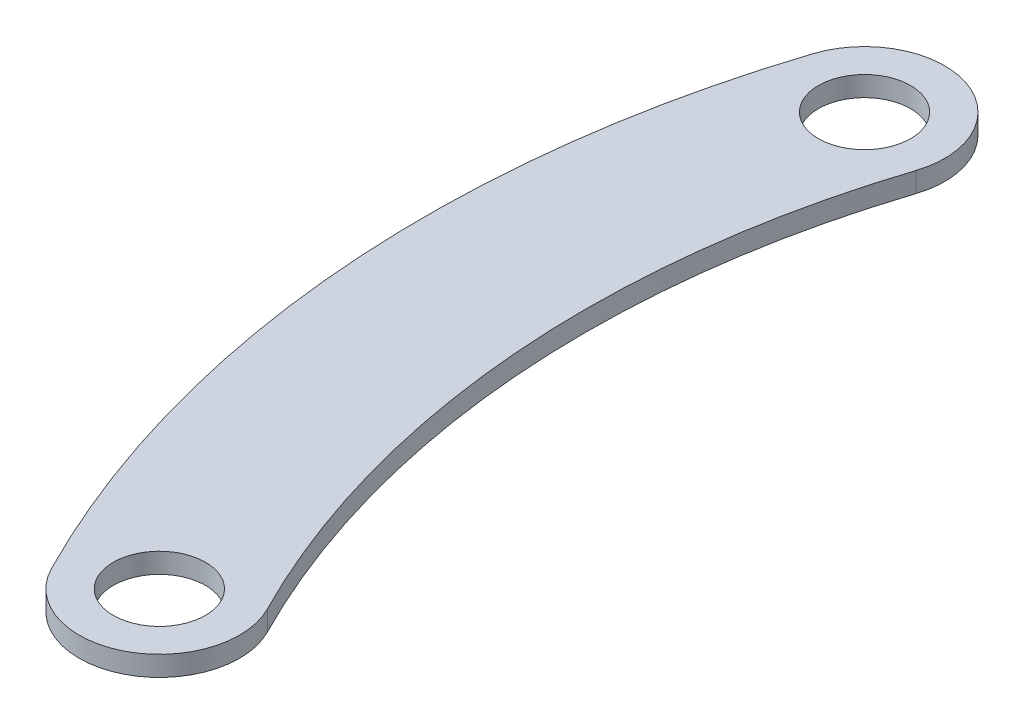
SolidWorks part; units mm, degrees
ref_plane "Front Plane" through (0, 0, 0) normal (0, 0, 1) x (1, 0, 0)
ref_plane "Top Plane" through (0, 0, 0) normal (0, 1, 0) x (1, 0, 0)
ref_plane "Right Plane" through (0, 0, 0) normal (1, 0, 0) x (0, 0, -1)
sketch "Sketch1" plane through (0, 0, 0) normal (0, 1, 0) x (1, 0, 0)
  line L0 (-142.6614, 46.3436) -> (0, 0) construction
  line L1 (0, 0) -> (-133.6467, -68.107) construction
  arc A0 (-133.6467, -68.107) -> (-142.6614, 46.3436) centre (0, 0) cw construction
  arc A1 (-154.0743, 50.0511) -> (-144.3384, -73.5555) centre (0, 0) ccw
  arc A2 (-131.2485, 42.6361) -> (-122.955, -62.6584) centre (0, 0) ccw
  arc A3 (-131.2485, 42.6361) -> (-154.0743, 50.0511) centre (-142.6614, 46.3436) ccw
  arc A4 (-144.3384, -73.5555) -> (-122.955, -62.6584) centre (-133.6467, -68.107) ccw
  circle A5 centre (-142.6614, 46.3436) radius 6
  circle A6 centre (-133.6467, -68.107) radius 6
  point P4 (-149.5369, -11.7783)
  dimension "D2" = 150
  dimension "D3" = 12
  dimension "D4" = 12
  dimension "D1" = 45
extrude "Boss-Extrude1" add sketch "Sketch1" along normal blind 3
scale "Scale1" scale about centroid uniform scaling yes scale factor 0.225
sketch "Sketch3" plane through (0, 1.8375, 0) normal (0, 1, 0) x (1, 0, 0)
  circle A0 centre (-144.5996, 1.5662) radius 1.55
  circle A1 centre (-142.5713, -24.1852) radius 1.55
  dimension "D1" = 3.1
  dimension "D2" = 3.1
extrude "Cut-Extrude2" cut sketch "Sketch3" against normal up to next
